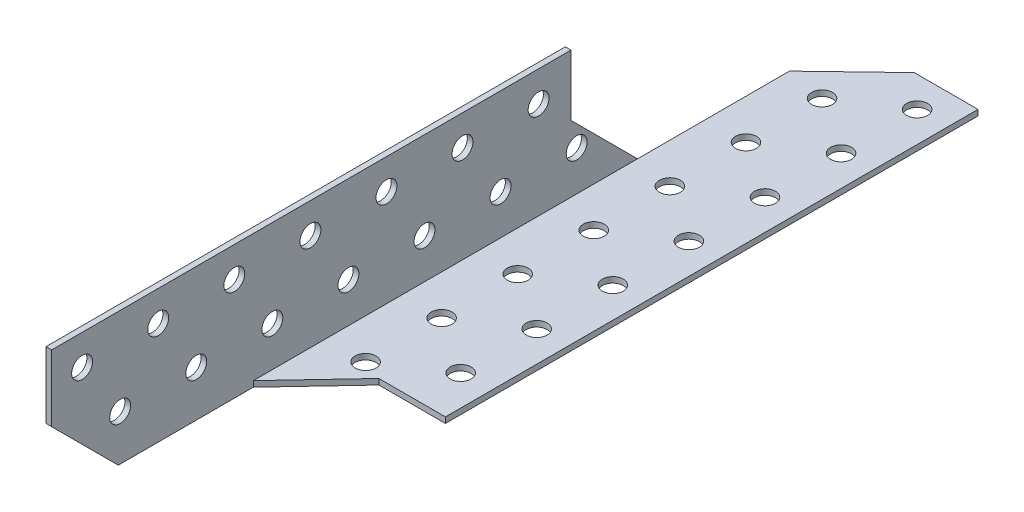
SolidWorks part; units mm, degrees
ref_plane "Płaszczyzna przednia" through (0, 0, 0) normal (0, 0, 1) x (1, 0, 0)
ref_plane "Płaszczyzna górna" through (0, 0, 0) normal (0, 1, 0) x (1, 0, 0)
ref_plane "Płaszczyzna prawa" through (0, 0, 0) normal (1, 0, 0) x (0, 0, -1)
sketch "Sketch1" plane through (0, 0, 0) normal (0, 0, 1) x (1, 0, 0)
  line L1 (-0.75, 17.5) -> (0.75, 17.5)
  line L2 (-0.75, 17.5) -> (-0.75, -17.5)
  line L3 (-0.75, -17.5) -> (0.75, -17.5)
  line L4 (0.75, 17.5) -> (0.75, -17.5)
  line L5 (-0.75, 17.5) -> (0.75, -17.5) construction
  line L6 (-0.75, -17.5) -> (0.75, 17.5) construction
  line L7 (-0.75, -17.5) -> (34.25, -17.5)
  line L8 (-0.75, -17.5) -> (-0.75, -16)
  line L9 (-0.75, -16) -> (34.25, -16)
  line L10 (34.25, -17.5) -> (34.25, -16)
  line L11 (-0.75, -17.5) -> (34.25, -16) construction
  line L12 (-0.75, -16) -> (34.25, -17.5) construction
  point P0 (0, 0)
  point P9 (16.75, -16.75)
  dimension "D1" = 1.5
  dimension "D2" = 35
  dimension "D3" = 1.5
  dimension "D4" = 35
extrude "Boss-Extrude1" add sketch "Sketch1" along normal blind 210 contours L2 L9 L4 L1 | L7 L10 L9 L4 | L9 L2 L3 L4
sketch "Sketch2" plane through (0, -16, 0) normal (0, 1, 0) x (1, 0, 0)
  line L0 (17.5, 0) -> (0.75, -16.0616)
  line L1 (0.75, 0) -> (34.25, 0) construction
  line L2 (-0.75, -210) -> (-0.75, 0) construction
  line L3 (17.5, 0) -> (-0.75, 0)
  line L4 (-0.75, 0) -> (-0.75, -17.5)
  line L5 (0.75, -16.0616) -> (0.75, -56)
  line L6 (0.75, -210) -> (0.75, 0) construction
  line L7 (0.75, -210) -> (0.75, 0) construction
  line L8 (34.25, -140) -> (-0.75, -140) construction
  line L9 (34.25, -210) -> (34.25, 0) construction
  line L10 (16.75, -140) -> (34.25, -140)
  line L11 (16.75, -140) -> (0.75, -157)
  line L12 (34.25, -140) -> (34.25, -210)
  line L13 (34.25, -210) -> (0.75, -210)
  line L14 (0.75, -210) -> (0.75, -157)
  line L15 (0.75, -56) -> (-0.75, -56)
  line L16 (-0.75, -56) -> (-0.75, -17.5)
  line L17 (-0.75, -56) -> (-0.75, -17.5)
  line M2 (34.25, 0) -> (0.75, 0)
  line M3 (0.75, 0) -> (0.75, -210)
  line M4 (0.75, -210) -> (34.25, -210)
  line M5 (34.25, -210) -> (34.25, 0)
  dimension "D1" = 17.5
  dimension "D2" = 140
  dimension "D3" = 17
  dimension "D4" = 56
extrude "Cut-Extrude7" cut sketch "Sketch2" against normal blind 52 and the other way blind 81 contours L0 M2 M3 | L16 L15 L3 L4 M3 | L10 L11 M3 M4 M5
sketch "Sketch4" plane through (0.75, 0, 0) normal (1, 0, 0) x (0, 0, -1)
  line L0 (-73.5, 1.5) -> (-56, -16)
  line L1 (-56, 17.5) -> (-56, -16) construction
  line L2 (-73.5, 1.5) -> (-73.5, 17.5)
  line L3 (-210, 17.5) -> (-56, 17.5) construction
  line L4 (-73.5, 17.5) -> (-56, 17.5)
  line L5 (-56, 17.5) -> (-56, -16)
  line L6 (-210, 0) -> (-192.5, -17.5)
  line L7 (-210, 17.5) -> (-210, -17.5) construction
  line L8 (-157, -17.5) -> (-210, -17.5) construction
  line L9 (-192.5, -17.5) -> (-210, -17.5)
  line L10 (-210, -17.5) -> (-210, 0)
  dimension "D1" = 17.5
  dimension "D2" = 17.5
extrude "Cut-Extrude8" cut sketch "Sketch4" against normal blind 52 and the other way blind 52
sketch "Sketch5" plane through (0.75, 0, 0) normal (1, 0, 0) x (0, 0, -1)
  line L0 (-72, -5.5) -> (-201.8481, -5.5) construction
  line L1 (-210, 17.5) -> (-73.5, 17.5) construction
  line L2 (-182, 9.5) -> (-182, -5.5) construction
  line L3 (-92.7452, -3.7009) -> (-92.7452, 11.2991) construction
  line L4 (-206.3168, 9.5) -> (-67.8637, 9.5) construction
  line L5 (-210, 17.5) -> (-210, 0) construction
  line L6 (-73.5, 1.5) -> (-73.5, 17.5) construction
  line L7 (-157, -17.5) -> (-192.5, -17.5) construction
  circle A0 centre (-72, -5.5) radius 2.75
  circle A1 centre (-92, -5.5) radius 2.75
  circle A2 centre (-112, -5.5) radius 2.75
  circle A3 centre (-132, -5.5) radius 2.75
  circle A4 centre (-152, -5.5) radius 2.75
  circle A5 centre (-172, -5.5) radius 2.75
  circle A6 centre (-192, -5.5) radius 2.75
  circle A14 centre (-202, 9.5) radius 2.75
  circle A15 centre (-182, 9.5) radius 2.75
  circle A16 centre (-162, 9.5) radius 2.75
  circle A17 centre (-142, 9.5) radius 2.75
  circle A18 centre (-122, 9.5) radius 2.75
  circle A19 centre (-102, 9.5) radius 2.75
  circle A20 centre (-82, 9.5) radius 2.75
  dimension "D1" = 20
  dimension "D2" = 20
  dimension "D3" = 20
  dimension "D4" = 20
  dimension "D5" = 20
  dimension "D6" = 20
  dimension "D7" = 8
  dimension "D8" = 20
  dimension "D9" = 20
  dimension "D10" = 20
  dimension "D11" = 20
  dimension "D12" = 20
  dimension "D13" = 20
  dimension "D14" = 20
  dimension "D15" = 15
  dimension "D16" = 8
  dimension "D17" = 8.5
  dimension "D18" = 8
  dimension "D19" = 10
  dimension "D20" = 10
  dimension "D21" = 12
extrude "Cut-Extrude9" cut sketch "Sketch5" against normal blind 52
sketch "Sketch6" plane through (0, -16, 0) normal (0, 1, 0) x (1, 0, 0)
  line L0 (26.25, -8) -> (26.25, -137.8481) construction
  line L1 (11.25, -118) -> (26.25, -118) construction
  line L2 (26.7861, -27.211) -> (11.7861, -27.211) construction
  line L3 (11.25, -142.3168) -> (11.25, -3.8637) construction
  line L4 (17.5, 0) -> (34.25, 0) construction
  line L5 (34.25, -140) -> (34.25, 0) construction
  circle A0 centre (26.25, -8) radius 2.75
  circle A1 centre (26.25, -28) radius 2.75
  circle A2 centre (26.25, -48) radius 2.75
  circle A3 centre (26.25, -68) radius 2.75
  circle A4 centre (26.25, -88) radius 2.75
  circle A5 centre (26.25, -108) radius 2.75
  circle A6 centre (26.25, -128) radius 2.75
  circle A7 centre (11.25, -138) radius 2.75
  circle A8 centre (11.25, -118) radius 2.75
  circle A9 centre (11.25, -98) radius 2.75
  circle A10 centre (11.25, -78) radius 2.75
  circle A11 centre (11.25, -58) radius 2.75
  circle A12 centre (11.25, -38) radius 2.75
  circle A13 centre (11.25, -18) radius 2.75
  dimension "D1" = 20
  dimension "D2" = 20
  dimension "D3" = 20
  dimension "D4" = 20
  dimension "D5" = 20
  dimension "D6" = 20
  dimension "D7" = 20
  dimension "D8" = 20
  dimension "D9" = 20
  dimension "D10" = 20
  dimension "D11" = 20
  dimension "D12" = 20
  dimension "D13" = 20
  dimension "D14" = 15
  dimension "D15" = 10
  dimension "D16" = 10
  dimension "D17" = 8
  dimension "D18" = 8
extrude "Cut-Extrude10" cut sketch "Sketch6" against normal blind 52
